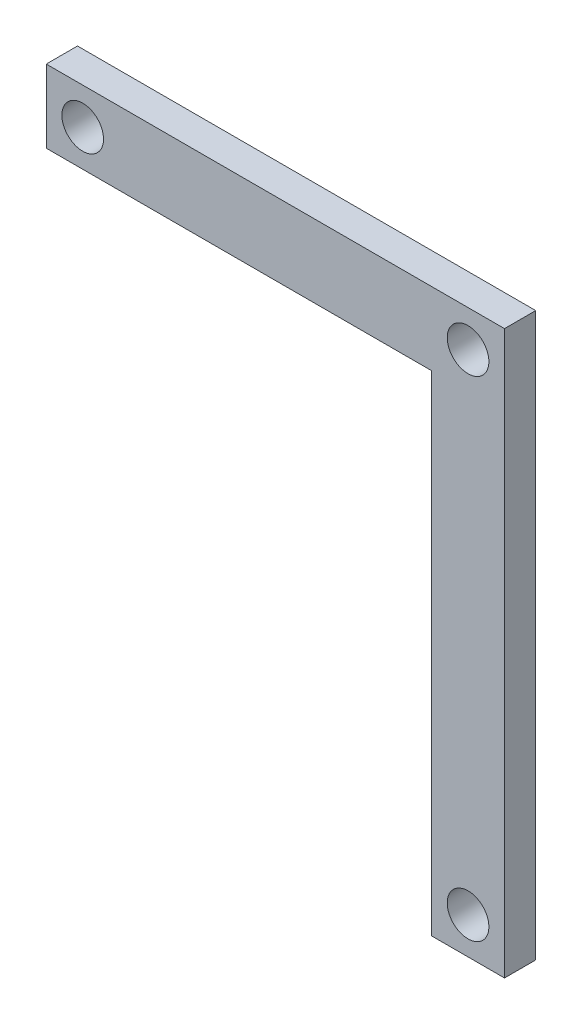
SolidWorks part; units mm, degrees
ref_plane "Front Plane" through (0, 0, 0) normal (0, 0, 1) x (1, 0, 0)
ref_plane "Top Plane" through (0, 0, 0) normal (0, 1, 0) x (1, 0, 0)
ref_plane "Right Plane" through (0, 0, 0) normal (1, 0, 0) x (0, 0, -1)
sketch "Sketch1" plane through (0, 0, 0) normal (0, 0, 1) x (1, 0, 0)
  line L0 (0, 0) -> (-220, 0)
  line L1 (-220, 0) -> (-220, -35)
  line L2 (-220, -35) -> (-35, -35)
  line L3 (-35, -35) -> (-35, -270)
  line L4 (-35, -270) -> (0, -270)
  line L5 (0, -270) -> (0, 0)
  dimension "D1" = 220
  dimension "D2" = 270
  dimension "D3" = 35
  dimension "D4" = 35
extrude "Boss-Extrude1" add sketch "Sketch1" along normal blind 15
sketch "Sketch2" plane through (0, 0, 15) normal (0, 0, 1) x (1, 0, 0)
  line L1 (0, -270) -> (0, 0) construction
  line L3 (0, 0) -> (-220, 0) construction
  line L4 (-35, 0) -> (0, -35) construction
  line L5 (-220, 0) -> (-185, -35) construction
  line L6 (-220, -35) -> (-35, -35) construction
  line L7 (0, -270) -> (-35, -235) construction
  line L8 (-35, -35) -> (-35, -270) construction
  point P0 (-17.5, -17.5)
  point P15 (-202.5, -17.5)
  point P22 (-17.5, -252.5)
  dimension "D1" = 35
  dimension "D2" = 35
  dimension "D3" = 35
  dimension "D4" = 35
hole_wizard "Ø20.0mm Dowel Hole2" positions "Sketch5" profile "Sketch6" hole size "Ø20.0" standard "ISO"
sketch "Sketch5" plane through (0, 0, 15) normal (0, 0, 1) x (1, 0, 0)
  point P0 (-17.5, -17.5)
  point P3 (-202.5, -17.5)
  point P6 (-17.5, -252.5)
sketch "Sketch6" plane through (-17.5, -17.5, 15) normal (1, 0, 0) x (0, -1, 0)
  line L0 (0, 0) -> (0, 28.2586)
  line L1 (0, 28.2586) -> (10, 22.25)
  line L2 (10, 22.25) -> (10, 0)
  line L5 (10, 0) -> (0, 0)
  line L10 (0, 28.2586) -> (-10, 22.25) construction
  line L11 (0, -6.35) -> (0, 107.95) construction
  dimension "Hole Dia." = 20
  dimension "Hole Depth" = 22.25
  dimension "Drill Angle" = 118
hole_wizard "Ø20.0mm Dowel Hole1" positions "Sketch3" profile "Sketch4" hole size "Ø20.0" standard "ISO"
sketch "Sketch3" plane through (0, 0, 15) normal (0, 0, 1) x (1, 0, 0)
  point P0 (-17.5, -17.5)
  point P3 (-202.5, -17.5)
  point P6 (-17.5, -252.5)
sketch "Sketch4" plane through (-17.5, -17.5, 15) normal (1, 0, 0) x (0, -1, 0)
  line L0 (0, 0) -> (0, 28.2586)
  line L1 (0, 28.2586) -> (10, 22.25)
  line L2 (10, 22.25) -> (10, 0)
  line L5 (10, 0) -> (0, 0)
  line L10 (0, 28.2586) -> (-10, 22.25) construction
  line L11 (0, -6.35) -> (0, 107.95) construction
  dimension "Hole Dia." = 20
  dimension "Hole Depth" = 22.25
  dimension "Drill Angle" = 118
